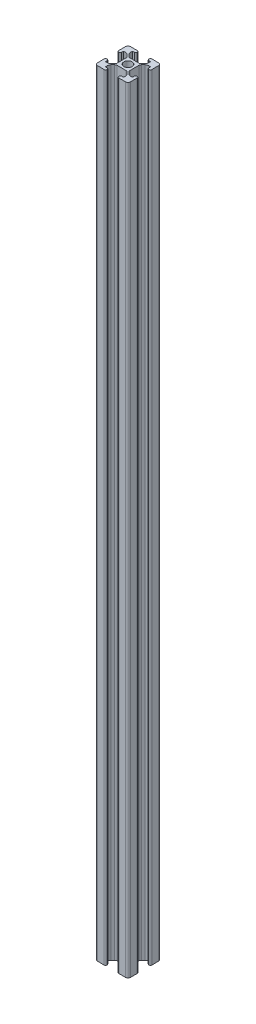
SolidWorks part; units mm, degrees
ref_plane "Front" through (0, 0, 0) normal (0, 0, 1) x (1, 0, 0)
ref_plane "Top" through (0, 0, 0) normal (0, 1, 0) x (1, 0, 0)
ref_plane "Right" through (0, 0, 0) normal (1, 0, 0) x (0, 0, -1)
sketch "Sketch2" plane through (0, 0, 0) normal (0, 1, 0) x (1, 0, 0)
  line L0 (-5.4, 4.8697) -> (-4.3393, 3.809)
  line L1 (-8.5, 10) -> (-4.4, 10)
  line L3 (-8.5, -10) -> (-4.4, -10)
  line L4 (10, 8.5) -> (10, 4.4)
  line L5 (-10, 10) -> (-9.5607, 9.5607) construction
  line L6 (-10, -10) -> (-9.5607, -9.5607) construction
  line L7 (-2.7483, 3.9) -> (2.7483, 3.9)
  line L8 (-3.9, 2.7483) -> (-3.9, -2.7483)
  line L9 (-2.7483, -3.9) -> (2.7483, -3.9)
  line L10 (3.9, 2.7483) -> (3.9, -2.7483)
  line L11 (-5.5, -8.2) -> (-4.4, -8.2)
  line L12 (-3.6, -9.2) -> (-3.6, -9)
  line L13 (-4.8697, 5.4) -> (-3.809, 4.3393)
  line L14 (4.8697, 5.4) -> (3.809, 4.3393)
  line L15 (5.4, 4.8697) -> (4.3393, 3.809)
  line L16 (-5.5, -8.2) -> (-5.5, -7.2)
  line L17 (9.5607, -9.5607) -> (10, -10) construction
  line L18 (-3.809, -4.3393) -> (-4.8697, -5.4)
  line L19 (-4.3393, -3.809) -> (-5.4, -4.8697)
  line L20 (3.809, -4.3393) -> (4.8697, -5.4)
  line L21 (4.3393, -3.809) -> (5.4, -4.8697)
  line L22 (9.5607, 9.5607) -> (10, 10) construction
  line L23 (8.5, -10) -> (4.4, -10)
  line L24 (3.6, -9.2) -> (3.6, -9)
  line L25 (5.5, -8.2) -> (4.4, -8.2)
  line L26 (0, 7.192) -> (0, -12.1556) construction
  line L27 (5.5, -8.2) -> (5.5, -7.2)
  line L28 (-8.2, 5.5) -> (-7.2, 5.5)
  line L29 (-8.2, 5.5) -> (-8.2, 4.4)
  line L30 (-10, 8.5) -> (-10, 4.4)
  line L31 (-8.2, -5.5) -> (-7.2, -5.5)
  line L32 (-10, -8.5) -> (-10, -4.4)
  line L33 (-8.2, -5.5) -> (-8.2, -4.4)
  line L34 (5.5, 8.2) -> (5.5, 7.2)
  line L35 (5.5, 8.2) -> (4.4, 8.2)
  line L36 (8.5, 10) -> (4.4, 10)
  line L37 (-5.5, 8.2) -> (-5.5, 7.2)
  line L38 (3.6, 9.2) -> (3.6, 9)
  line L39 (-5.5, 8.2) -> (-4.4, 8.2)
  line L40 (8.2, -5.5) -> (7.2, -5.5)
  line L41 (8.2, -5.5) -> (8.2, -4.4)
  line L42 (-3.6, 9.2) -> (-3.6, 9)
  line L43 (8.2, 5.5) -> (7.2, 5.5)
  line L44 (10, -4.4) -> (10, -8.5)
  line L45 (8.2, 5.5) -> (8.2, 4.4)
  line L46 (9, -3.6) -> (9.2, -3.6)
  line L47 (9, 3.6) -> (9.2, 3.6)
  line L48 (-9.2, 3.6) -> (-9, 3.6)
  line L49 (-9.2, -3.6) -> (-9, -3.6)
  line L52 (-8.5, 10) -> (-4.4, 10) [skipped]
  line L53 (10, -8.5) -> (10, -4.4) [skipped]
  line L54 (10, 8.5) -> (10, 4.4) [skipped]
  arc A0 (-10, -8.5) -> (-8.5, -10) centre (-8.5, -8.5) ccw
  arc A1 (8.5, -10) -> (10, -8.5) centre (8.5, -8.5) ccw
  arc A2 (8.5, 10) -> (10, 8.5) centre (8.5, 8.5) cw
  arc A3 (-8.5, 10) -> (-10, 8.5) centre (-8.5, 8.5) ccw
  arc A4 (-3.9, -2.7483) -> (-4.3393, -3.809) centre (-5.4, -2.7483) cw
  arc A5 (-2.7483, -3.9) -> (-3.809, -4.3393) centre (-2.7483, -5.4) ccw
  arc A6 (2.7483, -3.9) -> (3.809, -4.3393) centre (2.7483, -5.4) cw
  arc A7 (3.9, -2.7483) -> (4.3393, -3.809) centre (5.4, -2.7483) ccw
  arc A8 (3.9, 2.7483) -> (4.3393, 3.809) centre (5.4, 2.7483) cw
  arc A9 (2.7483, 3.9) -> (3.809, 4.3393) centre (2.7483, 5.4) ccw
  arc A10 (-2.7483, 3.9) -> (-3.809, 4.3393) centre (-2.7483, 5.4) cw
  arc A11 (-3.9, 2.7483) -> (-4.3393, 3.809) centre (-5.4, 2.7483) ccw
  arc A12 (-5.5, -7.2) -> (-4.8697, -5.4) centre (-2.6148, -7.2) cw
  arc A13 (-3.6, -9.2) -> (-4.4, -10) centre (-4.4, -9.2) cw
  arc A14 (-3.6, -9) -> (-4.4, -8.2) centre (-4.4, -9) ccw
  arc A15 (3.6, -9.2) -> (4.4, -10) centre (4.4, -9.2) ccw
  arc A16 (3.6, -9) -> (4.4, -8.2) centre (4.4, -9) cw
  arc A17 (5.5, -7.2) -> (4.8697, -5.4) centre (2.6148, -7.2) ccw
  arc A18 (-7.2, 5.5) -> (-5.4, 4.8697) centre (-7.2, 2.6148) cw
  arc A19 (-9, 3.6) -> (-8.2, 4.4) centre (-9, 4.4) ccw
  arc A20 (-9.2, 3.6) -> (-10, 4.4) centre (-9.2, 4.4) cw
  arc A21 (-7.2, -5.5) -> (-5.4, -4.8697) centre (-7.2, -2.6148) ccw
  arc A22 (-9, -3.6) -> (-8.2, -4.4) centre (-9, -4.4) cw
  arc A23 (-9.2, -3.6) -> (-10, -4.4) centre (-9.2, -4.4) ccw
  arc A24 (5.5, 7.2) -> (4.8697, 5.4) centre (2.6148, 7.2) cw
  arc A25 (3.6, 9) -> (4.4, 8.2) centre (4.4, 9) ccw
  arc A26 (3.6, 9.2) -> (4.4, 10) centre (4.4, 9.2) cw
  arc A27 (-5.5, 7.2) -> (-4.8697, 5.4) centre (-2.6148, 7.2) ccw
  arc A28 (-3.6, 9) -> (-4.4, 8.2) centre (-4.4, 9) cw
  arc A29 (-3.6, 9.2) -> (-4.4, 10) centre (-4.4, 9.2) ccw
  arc A30 (7.2, -5.5) -> (5.4, -4.8697) centre (7.2, -2.6148) cw
  arc A31 (9, -3.6) -> (8.2, -4.4) centre (9, -4.4) ccw
  arc A32 (9.2, -3.6) -> (10, -4.4) centre (9.2, -4.4) cw
  arc A33 (7.2, 5.5) -> (5.4, 4.8697) centre (7.2, 2.6148) ccw
  arc A34 (9, 3.6) -> (8.2, 4.4) centre (9, 4.4) cw
  arc A35 (9.2, 3.6) -> (10, 4.4) centre (9.2, 4.4) ccw
  circle A36 centre (0, 0) radius 2.5
  point P0 (0, 0)
  point P6 (0, 0)
  point P41 (-3.9, -3.3697)
  point P44 (-3.3697, -3.9)
  point P47 (3.3697, -3.9)
  point P50 (3.9, -3.3697)
  dimension "D5" = 1.5
  dimension "D3" = 1.5
  dimension "D9" = 0.8
  dimension "D1" = 20
  dimension "D2" = 20
  dimension "D4" = 4
  dimension "D6" = 0.75
  dimension "D8" = 1.8
  dimension "D10" = 1
  dimension "D7" = 2
extrude "Boss-Extrude1" add sketch "Sketch2" along normal blind 470
